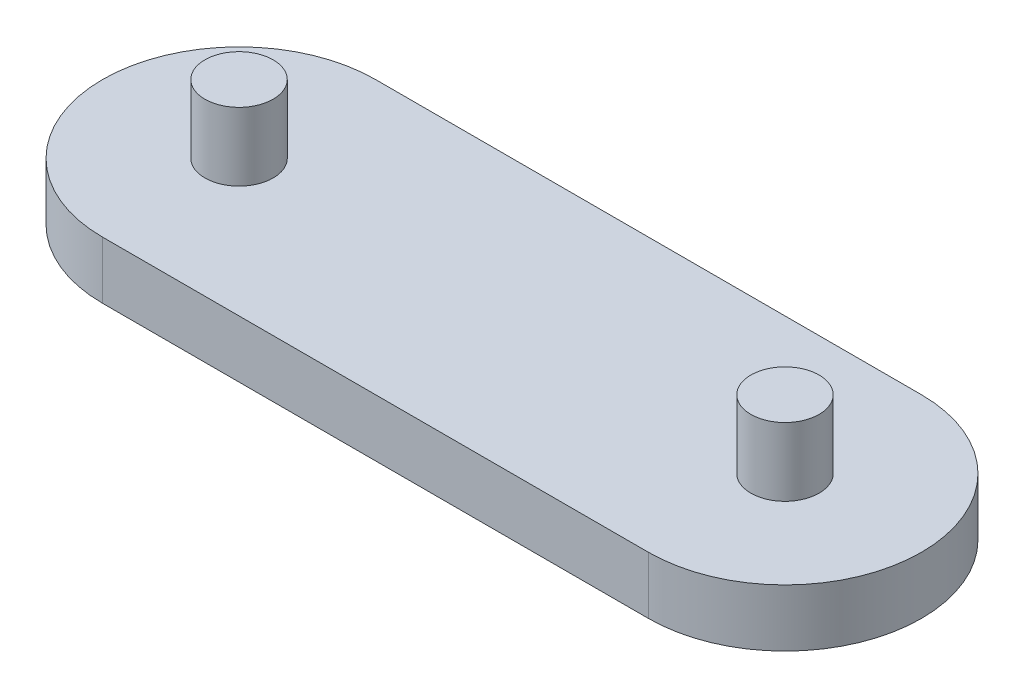
SolidWorks part; units mm, degrees
ref_plane "Front Plane" through (0, 0, 0) normal (0, 0, 1) x (1, 0, 0)
ref_plane "Top Plane" through (0, 0, 0) normal (0, 1, 0) x (1, 0, 0)
ref_plane "Right Plane" through (0, 0, 0) normal (1, 0, 0) x (0, 0, -1)
sketch "Sketch2" plane through (0, 0, 0) normal (0, 1, 0) x (1, 0, 0)
  line L0 (0, 0) -> (-400, 0) construction
  line L1 (0, -100) -> (-400, -100)
  line L2 (0, 100) -> (-400, 100)
  arc A0 (0, -100) -> (0, 100) centre (0, 0) ccw
  arc A1 (-400, 100) -> (-400, -100) centre (-400, 0) ccw
  point P3 (-200, 0)
extrude "Boss-Extrude1" add sketch "Sketch2" along normal blind 42
sketch "Sketch3" plane through (0, 42, 0) normal (0, 1, 0) x (1, 0, 0)
  circle A0 centre (0, 0) radius 25
  point P3 (-496.0473, -571.3887)
extrude "Boss-Extrude2" add sketch "Sketch3" along normal blind 50
sketch "Sketch4" plane through (0, 42, 0) normal (0, 1, 0) x (1, 0, 0)
  circle A0 centre (-400, 0) radius 25
extrude "Boss-Extrude3" add sketch "Sketch4" along normal blind 50
